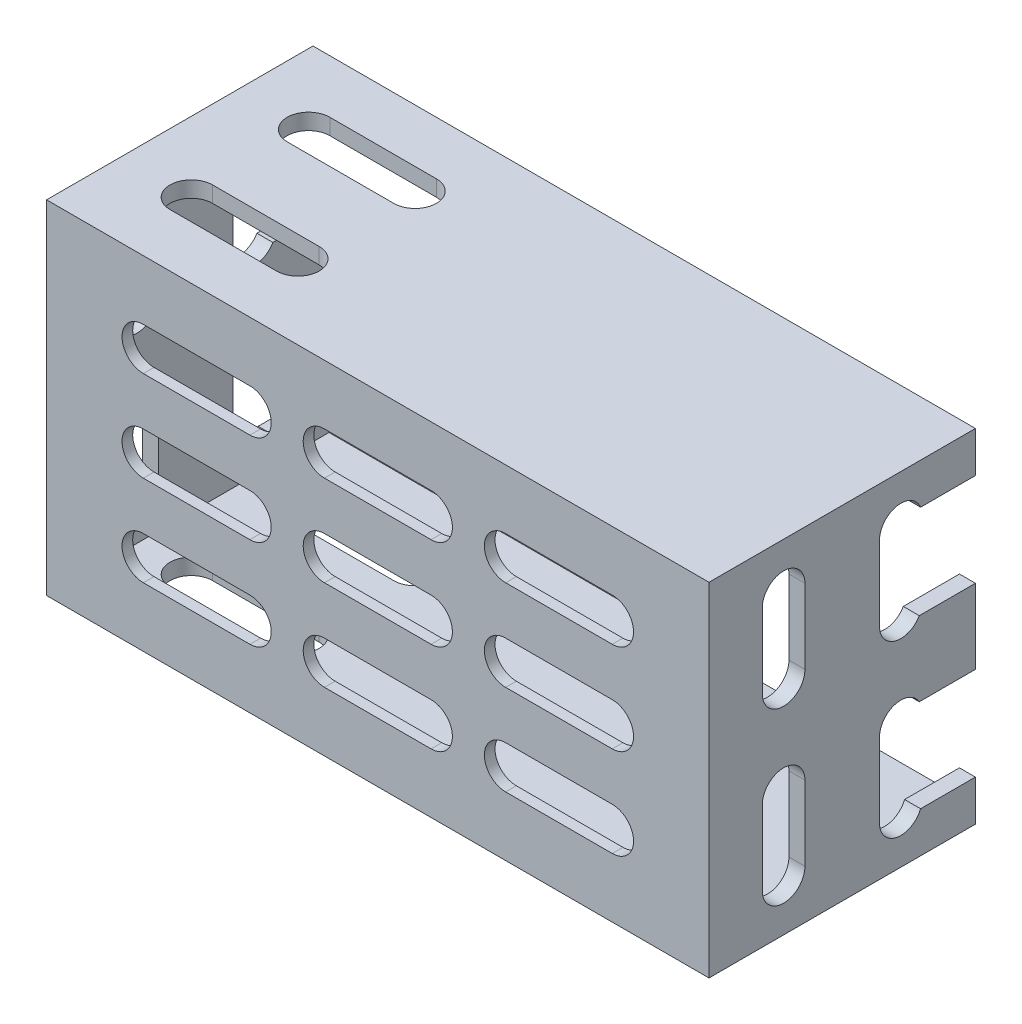
SolidWorks part; units mm, degrees
ref_plane "Front Plane" through (0, 0, 0) normal (0, 0, 1) x (1, 0, 0)
ref_plane "Top Plane" through (0, 0, 0) normal (0, 1, 0) x (1, 0, 0)
ref_plane "Right Plane" through (0, 0, 0) normal (1, 0, 0) x (0, 0, -1)
sketch "Sketch1" plane through (0, 0, 0) normal (0, 0, 1) x (1, 0, 0)
  line L4 (29.58, -14.58) -> (-29.58, -14.58)
  line L5 (29.25, -14.25) -> (-29.25, -14.25) construction
  line L6 (29.25, -14.25) -> (29.25, 14.25) construction
  line L7 (29.25, 14.25) -> (-29.25, 14.25) construction
  line L16 (-29.25, -14.25) -> (-29.25, 14.25) construction
  line L17 (-29.58, -14.58) -> (-29.58, 14.58)
  line L18 (29.58, 14.58) -> (-29.58, 14.58)
  line L19 (29.58, -14.58) -> (29.58, 14.58)
  line L20 (-31.08, -16.08) -> (-31.08, 16.08)
  line L21 (31.08, 16.08) -> (-31.08, 16.08)
  line L22 (31.08, -16.08) -> (31.08, 16.08)
  line L23 (31.08, -16.08) -> (-31.08, -16.08)
  dimension "D1" = 0.33
  dimension "D2" = 1.5
extrude "Boss-Extrude1" add sketch "Sketch1" along normal blind 19
sketch "Sketch2" plane through (0, 0, 19) normal (0, 0, 1) x (1, 0, 0)
  line L4 (-31.08, -16.08) -> (31.08, -16.08)
  line L5 (-31.08, -16.08) -> (31.08, -16.08)
  line L6 (-31.08, 16.08) -> (-31.08, -16.08)
  line L7 (31.08, 16.08) -> (-31.08, 16.08)
  line L10 (-31.08, 16.08) -> (-31.08, -16.08)
  line L11 (31.08, 16.08) -> (-31.08, 16.08)
  line L12 (31.08, -16.08) -> (31.08, 16.08)
  line L13 (31.08, -16.08) -> (31.08, 16.08)
  dimension "D1" = 0
extrude "Boss-Extrude2" add sketch "Sketch2" along normal blind 1
sketch "Sketch3" plane through (0, 0, 0) normal (0, 0, -1) x (-1, 0, 0)
  line L1 (29.58, -14.58) -> (-29.58, -14.58) construction
  line L4 (-31.08, -16.08) -> (31.08, -16.08)
  line L5 (31.08, 16.08) -> (-31.08, 16.08)
  line L6 (31.08, -16.08) -> (31.08, 16.08)
  line L7 (-31.08, -16.08) -> (31.08, -16.08)
  line L9 (31.08, 16.08) -> (9, 16.08)
  line L10 (31.08, -16.08) -> (31.08, 16.08)
  line L14 (29.58, 14.58) -> (29.58, -14.58) construction
  line L20 (-29.58, 14.58) -> (29.58, 14.58) construction
  line L21 (-29.58, -14.58) -> (-29.58, 14.58) construction
  line L22 (29.58, -14.58) -> (-29.58, -14.58)
  line L23 (29.58, 14.58) -> (29.58, -14.58)
  line L24 (-31.08, 16.08) -> (-31.08, -16.08)
  line L25 (-31.08, 16.08) -> (-31.08, -16.08)
  line L26 (-29.58, 14.58) -> (-9, 14.58)
  line L27 (-29.58, -14.58) -> (-29.58, 14.58)
  line L30 (-9, 16.08) -> (-31.08, 16.08)
  line L31 (9, 14.58) -> (29.58, 14.58)
  line L32 (-9, 16.08) -> (9, 16.08)
  line L33 (9, 14.58) -> (-9, 14.58)
  dimension "D1" = 0
extrude "Boss-Extrude3" add sketch "Sketch3" along normal up to surface (5 mm away)
sketch "Sketch8" plane through (0, 0, 19) normal (0, 0, -1) x (-1, 0, 0)
  line L0 (12, 6.5) -> (22, 6.5) construction
  line L1 (12, -2) -> (22, -2) construction
  line L2 (12, -10.5) -> (22, -10.5) construction
  line L3 (-5, -10.5) -> (5, -10.5) construction
  line L4 (-22, -10.5) -> (-12, -10.5) construction
  line L5 (-22, -2) -> (-12, -2) construction
  line L6 (-5, 6.5) -> (5, 6.5) construction
  line L7 (-22, 6.5) -> (-12, 6.5) construction
  line L8 (12, 6.5) -> (22, 6.5)
  line L9 (12, -2) -> (22, -2)
  line L10 (12, -10.5) -> (22, -10.5)
  line L11 (-5, -10.5) -> (5, -10.5)
  line L12 (-22, -10.5) -> (-12, -10.5)
  line L13 (-22, -2) -> (-12, -2)
  line L14 (-5, 6.5) -> (5, 6.5)
  line L15 (-22, 6.5) -> (-12, 6.5)
  line L16 (22, -6.5) -> (12, -6.5) construction
  line L17 (5, -6.5) -> (-5, -6.5) construction
  line L18 (-12, -6.5) -> (-22, -6.5) construction
  line L19 (22, 2) -> (12, 2) construction
  line L20 (-5, -2) -> (5, -2) construction
  line L21 (5, 2) -> (-5, 2) construction
  line L22 (-12, 2) -> (-22, 2) construction
  line L23 (22, 10.5) -> (12, 10.5) construction
  line L24 (5, 10.5) -> (-5, 10.5) construction
  line L25 (-12, 10.5) -> (-22, 10.5) construction
  line L26 (22, -6.5) -> (12, -6.5)
  line L27 (5, -6.5) -> (-5, -6.5)
  line L28 (-12, -6.5) -> (-22, -6.5)
  line L29 (22, 2) -> (12, 2)
  line L30 (-5, -2) -> (5, -2)
  line L31 (5, 2) -> (-5, 2)
  line L32 (-12, 2) -> (-22, 2)
  line L33 (22, 10.5) -> (12, 10.5)
  line L34 (5, 10.5) -> (-5, 10.5)
  line L35 (-12, 10.5) -> (-22, 10.5)
  arc A0 (22, -10.5) -> (22, -6.5) centre (22, -8.5) ccw construction
  arc A1 (12, -6.5) -> (12, -10.5) centre (12, -8.5) ccw construction
  arc A2 (5, -10.5) -> (5, -6.5) centre (5, -8.5) ccw construction
  arc A3 (-5, -6.5) -> (-5, -10.5) centre (-5, -8.5) ccw construction
  arc A4 (-12, -10.5) -> (-12, -6.5) centre (-12, -8.5) ccw construction
  arc A5 (-22, -6.5) -> (-22, -10.5) centre (-22, -8.5) ccw construction
  arc A6 (22, -2) -> (22, 2) centre (22, 0) ccw construction
  arc A7 (12, 2) -> (12, -2) centre (12, 0) ccw construction
  arc A8 (-5, 2) -> (-5, -2) centre (-5, 0) ccw construction
  arc A9 (5, -2) -> (5, 2) centre (5, 0) ccw construction
  arc A10 (-12, -2) -> (-12, 2) centre (-12, 0) ccw construction
  arc A11 (-22, 2) -> (-22, -2) centre (-22, 0) ccw construction
  arc A12 (22, 6.5) -> (22, 10.5) centre (22, 8.5) ccw construction
  arc A13 (12, 10.5) -> (12, 6.5) centre (12, 8.5) ccw construction
  arc A14 (-5, 10.5) -> (-5, 6.5) centre (-5, 8.5) ccw construction
  arc A15 (-12, 6.5) -> (-12, 10.5) centre (-12, 8.5) ccw construction
  arc A16 (-22, 10.5) -> (-22, 6.5) centre (-22, 8.5) ccw construction
  arc A17 (22, -10.5) -> (22, -6.5) centre (22, -8.5) ccw
  arc A18 (12, -6.5) -> (12, -10.5) centre (12, -8.5) ccw
  arc A19 (5, -10.5) -> (5, -6.5) centre (5, -8.5) ccw
  arc A20 (-5, -6.5) -> (-5, -10.5) centre (-5, -8.5) ccw
  arc A21 (-12, -10.5) -> (-12, -6.5) centre (-12, -8.5) ccw
  arc A22 (-22, -6.5) -> (-22, -10.5) centre (-22, -8.5) ccw
  arc A23 (22, -2) -> (22, 2) centre (22, 0) ccw
  arc A24 (12, 2) -> (12, -2) centre (12, 0) ccw
  arc A25 (-5, 2) -> (-5, -2) centre (-5, 0) ccw
  arc A26 (5, -2) -> (5, 2) centre (5, 0) ccw
  arc A27 (-12, -2) -> (-12, 2) centre (-12, 0) ccw
  arc A28 (-22, 2) -> (-22, -2) centre (-22, 0) ccw
  arc A29 (22, 6.5) -> (22, 10.5) centre (22, 8.5) ccw
  arc A30 (12, 10.5) -> (12, 6.5) centre (12, 8.5) ccw
  arc A31 (-5, 10.5) -> (-5, 6.5) centre (-5, 8.5) ccw
  arc A32 (-12, 6.5) -> (-12, 10.5) centre (-12, 8.5) ccw
  arc A33 (-22, 10.5) -> (-22, 6.5) centre (-22, 8.5) ccw
  arc A34 (5, 6.5) -> (5, 10.5) centre (5, 8.5) ccw construction
  arc A35 (5, 6.5) -> (5, 10.5) centre (5, 8.5) ccw
extrude "Cut-Extrude4" cut sketch "Sketch8" against normal through all
sketch "Sketch5" plane through (-15, 16.08, 0) normal (0, -1, 0) x (1, 0, 0)
  line L0 (-9.5, 2) -> (0.5, 2) construction
  line L1 (-9.5, 4) -> (0.5, 4)
  line L2 (-9.5, 0) -> (0.5, 0)
  line L3 (-16.08, 7.5) -> (46.08, 7.5) construction
  line L4 (46.08, -5) -> (-16.08, -5) construction
  line L5 (-16.08, 20) -> (46.08, 20) construction
  line L6 (15, -5) -> (15, 20) construction
  line L7 (46.08, 13) -> (-16.08, 13) construction
  line L8 (-16.08, 20) -> (-16.08, -5) construction
  line L9 (-4.5, 20) -> (-4.5, -5) construction
  line L10 (46.08, 2) -> (-16.08, 2) construction
  line L11 (34.5, 20) -> (34.5, -5) construction
  line L13 (10, -32.735) -> (20, -32.735)
  line L14 (10, -28.735) -> (20, -28.735)
  line L15 (10, -30.735) -> (20, -30.735) construction
  line L16 (29.5, -65.4699) -> (39.5, -65.4699)
  line L17 (29.5, -61.4699) -> (39.5, -61.4699)
  line L18 (29.5, -63.4699) -> (39.5, -63.4699) construction
  line L19 (10, -21.735) -> (20, -21.735)
  line L20 (10, -17.735) -> (20, -17.735)
  line L21 (10, -19.735) -> (20, -19.735) construction
  line L22 (29.5, -54.4699) -> (39.5, -54.4699)
  line L23 (29.5, -50.4699) -> (39.5, -50.4699)
  line L24 (29.5, -52.4699) -> (39.5, -52.4699) construction
  line L25 (-9.5, 11) -> (0.5, 11)
  line L26 (-9.5, 15) -> (0.5, 15)
  line L27 (-9.5, 13) -> (0.5, 13) construction
  line L28 (46.08, 20) -> (46.08, -5) construction
  arc A0 (-9.5, 4) -> (-9.5, 0) centre (-9.5, 2) ccw
  arc A1 (0.5, 0) -> (0.5, 4) centre (0.5, 2) ccw
  arc A2 (10, -28.735) -> (10, -32.735) centre (10, -30.735) ccw
  arc A3 (20, -32.735) -> (20, -28.735) centre (20, -30.735) ccw
  arc A4 (29.5, -61.4699) -> (29.5, -65.4699) centre (29.5, -63.4699) ccw
  arc A5 (39.5, -65.4699) -> (39.5, -61.4699) centre (39.5, -63.4699) ccw
  arc A6 (10, -17.735) -> (10, -21.735) centre (10, -19.735) ccw
  arc A7 (20, -21.735) -> (20, -17.735) centre (20, -19.735) ccw
  arc A8 (29.5, -50.4699) -> (29.5, -54.4699) centre (29.5, -52.4699) ccw
  arc A9 (39.5, -54.4699) -> (39.5, -50.4699) centre (39.5, -52.4699) ccw
  arc A10 (-9.5, 15) -> (-9.5, 11) centre (-9.5, 13) ccw
  arc A11 (0.5, 11) -> (0.5, 15) centre (0.5, 13) ccw
  point P2 (-4.5, 2)
  point P9 (0, 0)
  point P15 (46.08, 7.5)
  point P17 (0, 0)
  point P18 (20, -21.735)
  point P29 (15, -5)
  point P31 (15, -30.735)
  point P38 (34.5, -63.4699)
  point P45 (15, -19.735)
  point P52 (34.5, -52.4699)
  point P59 (-4.5, 13)
  dimension "D1" = 10
  dimension "D2" = 4
  dimension "D3" = 39
  dimension "D4" = 11
  dimension "D5" = 3
  dimension "D6" = 2
extrude "Cut-Extrude2" cut sketch "Sketch5" along normal through all
sketch "Sketch7" plane through (31.08, -15, 0) normal (-1, 0, 0) x (0, 0, -1)
  line L0 (-13, -26.5) -> (-13, -19.5) construction
  line L1 (-15, -26.5) -> (-15, -19.5)
  line L2 (-11, -26.5) -> (-11, -19.5)
  line L3 (-20, -15) -> (5, -15) construction
  line L4 (-20, -31.08) -> (-20, 1.08) construction
  line L5 (5, 1.08) -> (5, -31.08) construction
  line L6 (-7.5, 1.08) -> (-7.5, -31.08) construction
  line L7 (-20, 1.08) -> (5, 1.08) construction
  line L8 (-20, -31.08) -> (5, -31.08) construction
  line L9 (-13, -31.08) -> (-13, 1.08) construction
  line L10 (-20, -7) -> (5, -7) construction
  line L11 (-20, -23) -> (5, -23) construction
  line L12 (-2, -31.08) -> (-2, 1.08) construction
  line L13 (0, -26.5) -> (0, -19.5)
  line L14 (-4, -26.5) -> (-4, -19.5)
  line L15 (-2, -26.5) -> (-2, -19.5) construction
  line L16 (0, -10.5) -> (0, -3.5)
  line L17 (-4, -10.5) -> (-4, -3.5)
  line L18 (-2, -10.5) -> (-2, -3.5) construction
  line L19 (-11, -10.5) -> (-11, -3.5)
  line L20 (-15, -10.5) -> (-15, -3.5)
  line L21 (-13, -10.5) -> (-13, -3.5) construction
  arc A0 (-15, -26.5) -> (-11, -26.5) centre (-13, -26.5) ccw
  arc A1 (-11, -19.5) -> (-15, -19.5) centre (-13, -19.5) ccw
  arc A2 (-4, -26.5) -> (0, -26.5) centre (-2, -26.5) ccw
  arc A3 (0, -19.5) -> (-4, -19.5) centre (-2, -19.5) ccw
  arc A4 (-4, -10.5) -> (0, -10.5) centre (-2, -10.5) ccw
  arc A5 (0, -3.5) -> (-4, -3.5) centre (-2, -3.5) ccw
  arc A6 (-15, -10.5) -> (-11, -10.5) centre (-13, -10.5) ccw
  arc A7 (-11, -3.5) -> (-15, -3.5) centre (-13, -3.5) ccw
  point P2 (-13, -23)
  point P16 (-20, -15)
  point P32 (-2, -23)
  point P39 (-2, -7)
  point P46 (-13, -7)
  dimension "D1" = 7
  dimension "D2" = 4
  dimension "D3" = 16
  dimension "D6" = 11
  dimension "D4" = 2
  dimension "D5" = 2
extrude "Cut-Extrude3" cut sketch "Sketch7" along normal through all
sketch "Sketch9" plane through (-31.08, 0, 0) normal (-1, 0, 0) x (0, 0, 1)
  line L0 (-5, 0) -> (20, 0) construction
  line L1 (-5, 3.5) -> (2, 3.5)
  line L2 (-5, 3.5) -> (-5, 12.25)
  line L3 (-5, 12.25) -> (2, 12.25)
  line L4 (2, 3.5) -> (2, 12.25)
  line L6 (-5, -16.08) -> (-5, 16.08) construction
  line L7 (20, 16.08) -> (20, -16.08) construction
  line L8 (2, -3.5) -> (2, -12.25)
  line L9 (-5, -12.25) -> (2, -12.25)
  line L10 (-5, -3.5) -> (-5, -12.25)
  line L11 (-5, -3.5) -> (2, -3.5)
  arc A0 (4, 11.5) -> (0, 11.5) centre (2, 11.5) ccw construction
  point P22 (2, 13.5)
extrude "Cut-Extrude5" cut sketch "Sketch9" against normal through all
